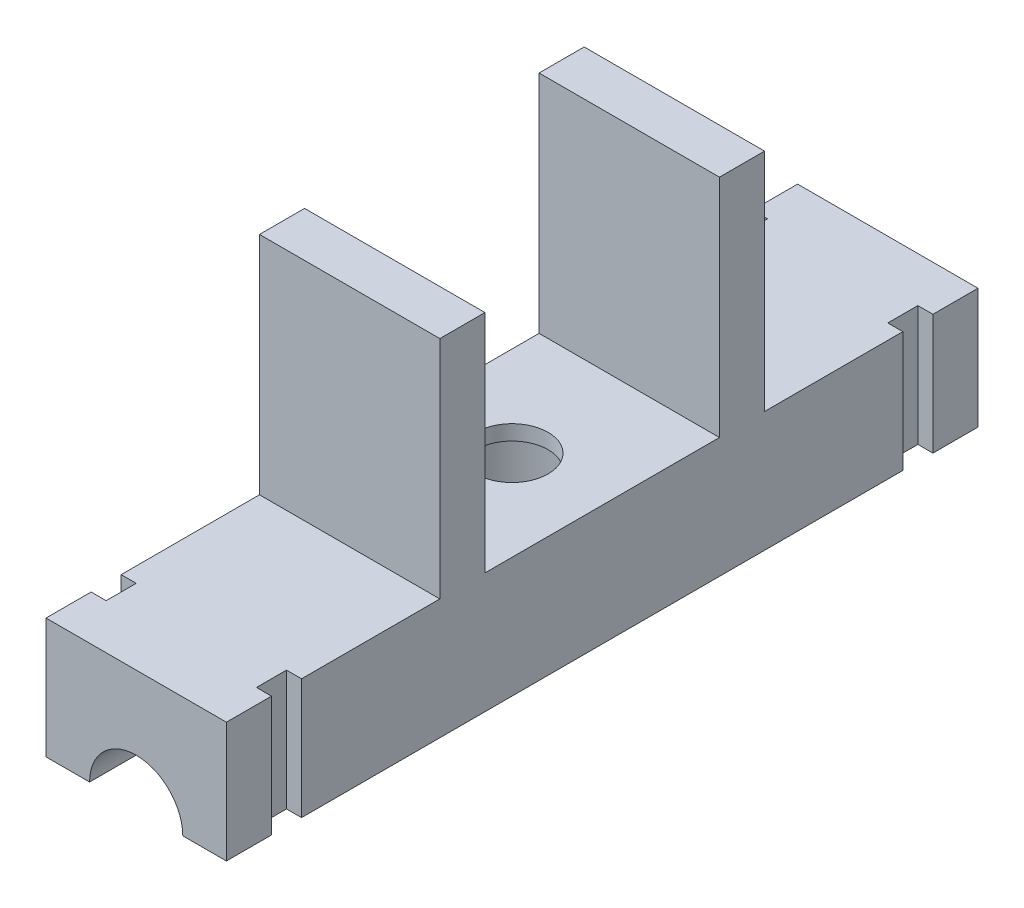
SolidWorks part; units mm, degrees
ref_plane "Front Plane" through (0, 0, 0) normal (0, 0, 1) x (1, 0, 0)
ref_plane "Top Plane" through (0, 0, 0) normal (0, 1, 0) x (1, 0, 0)
ref_plane "Right Plane" through (0, 0, 0) normal (1, 0, 0) x (0, 0, -1)
sketch "Sketch4" plane through (0, 0, 0) normal (1, 0, 0) x (0, 0, -1)
  line L0 (0, 0) -> (0, 20.951)
  line L1 (25, 0) -> (-25, 0)
  line L2 (-25, 0) -> (-25, 8)
  line L3 (-25, 8) -> (-10.8, 8)
  line L4 (-10.8, 8) -> (-10.8, 23)
  line L5 (-10.8, 23) -> (-7.8, 23)
  line L6 (-7.8, 23) -> (-7.8, 8)
  line L7 (-7.8, 8) -> (7.8, 8)
  line L8 (25, 8) -> (10.8, 8)
  line L9 (25, 0) -> (25, 8)
  line L10 (10.8, 23) -> (7.8, 23)
  line L11 (10.8, 8) -> (10.8, 23)
  line L12 (7.8, 23) -> (7.8, 8)
  point P16 (0, 8)
  dimension "D1" = 7.8
  dimension "D2" = 3
  dimension "D3" = 25
  dimension "D4" = 8
  dimension "D5" = 15
extrude "Boss-Extrude1" add sketch "Sketch4" along normal blind 12 contours L7 L6 L5 L4 L3 L2 L1 L0 | L10 L12 L7 L0 L1 L9 L8 L11
hole_wizard "CBORE for M4 Pan Head Machine Screw1" positions "Sketch7" profile "Sketch6" counterbore size "M4" standard "ANSI Metric" end condition through all
sketch "Sketch7" plane through (0, 0, 0) normal (0, -1, 0) x (-1, 0, 0)
  point P0 (-6, 0)
sketch "Sketch6" plane through (6, 0, 0) normal (1, 0, 0) x (0, 0, -1)
  line L0 (0, 0) -> (0, 23)
  line L1 (0, 23) -> (2.4, 23)
  line L3 (2.4, 23) -> (2.4, 7)
  line L4 (2.4, 7) -> (4.5, 7)
  line L5 (4.5, 7) -> (4.5, 0)
  line L7 (4.5, 0) -> (0, 0)
  line L11 (0, -6.35) -> (0, 107.95) construction
  dimension "Thru Hole Dia." = 4.8
  dimension "Thru Hole Depth" = 23
  dimension "C'Bore Dia." = 9
  dimension "C'Bore Depth" = 7
hole_wizard "Ø6.0mm Dowel Hole1" positions "Sketch11" profile "Sketch12" hole size "Ø6.0" standard "ANSI Metric" end condition through all
sketch "Sketch11" plane through (0, 0, 25) normal (0, 0, 1) x (1, 0, 0)
  line L0 (12, 0) -> (0, 0) construction
  point P0 (6, 0)
sketch "Sketch12" plane through (6, 0, 25) normal (1, 0, 0) x (0, -1, 0)
  line L0 (0, 0) -> (0, 50)
  line L1 (0, 50) -> (3.1, 50)
  line L2 (3.1, 50) -> (3.1, 0)
  line L5 (3.1, 0) -> (0, 0)
  line L11 (0, -6.35) -> (0, 107.95) construction
  dimension "Thru Hole Dia." = 6.2
  dimension "Thru Hole Depth" = 50
sketch "Sketch13" plane through (0, 0, 0) normal (0, -1, 0) x (1, 0, 0)
  line L0 (0, -25) -> (0, 25) construction
  line L1 (0, -22) -> (1, -22)
  line L2 (0, -22) -> (0, -20)
  line L3 (0, -20) -> (1, -20)
  line L4 (1, -22) -> (1, -20)
  line L5 (0, 0) -> (12, 0)
  line L6 (12, -25) -> (12, 25) construction
  line L7 (6, 0) -> (6, 5.9981)
  line L8 (0, 20) -> (1, 20)
  line L9 (1, 22) -> (1, 20)
  line L10 (0, 22) -> (1, 22)
  line L11 (0, 22) -> (0, 20)
  line L12 (12, -20) -> (11, -20)
  line L13 (11, -22) -> (11, -20)
  line L14 (12, -22) -> (11, -22)
  line L15 (12, -22) -> (12, -20)
  line L16 (12, 22) -> (12, 20)
  line L17 (12, 22) -> (11, 22)
  line L18 (11, 22) -> (11, 20)
  line L19 (12, 20) -> (11, 20)
  line M13 (0, 25) -> (0, -25)
extrude "Cut-Extrude1" cut sketch "Sketch13" against normal blind 12 contours L1 L4 L3 M13 | L10 L8 L9 M13 | L19 L16 L17 L18 | L14 L15 L12 L13
